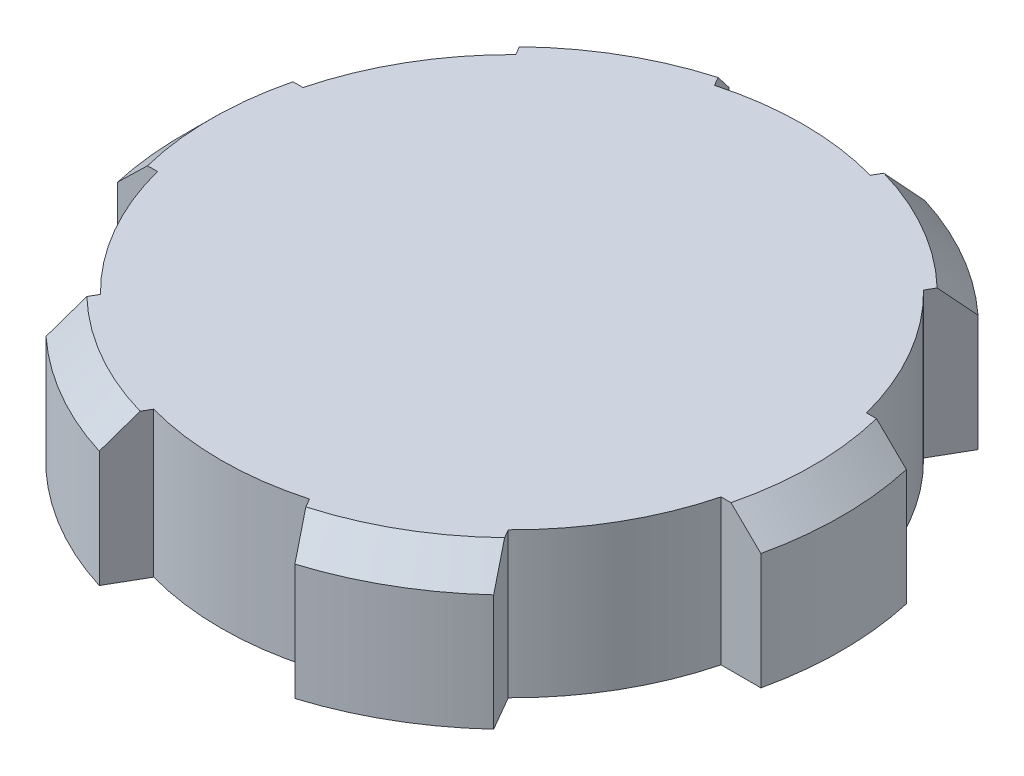
SolidWorks part; units mm, degrees
ref_plane "前视基准面" through (0, 0, 0) normal (0, 0, 1) x (1, 0, 0)
ref_plane "上视基准面" through (0, 0, 0) normal (0, 1, 0) x (1, 0, 0)
ref_plane "右视基准面" through (0, 0, 0) normal (1, 0, 0) x (0, 0, -1)
sketch "草图1" plane through (0, 0, 0) normal (0, 1, 0) x (1, 0, 0)
  circle A0 centre (0, 0) radius 10
  dimension "D1" = 20
extrude "凸台-拉伸1" add sketch "草图1" along normal blind 5
sketch "草图2" plane through (0, 5, 0) normal (0, 1, 0) x (1, 0, 0)
  line L0 (9.6825, 2.5) -> (11.0528, 2.5)
  line L1 (-11.0528, -2.5) -> (-9.6825, -2.5)
  line L3 (-11.0528, 2.5) -> (-9.6825, 2.5)
  line L5 (-11.0528, -2.5) -> (-9.7536, -2.2061) construction
  line L6 (-11.0528, 2.5) -> (-9.7536, 2.2061) construction
  line L7 (9.7536, 2.2061) -> (11.0528, 2.5) construction
  line L8 (9.7536, -2.2061) -> (11.0528, -2.5) construction
  line L9 (9.6825, -2.5) -> (11.0528, -2.5)
  arc A0 (-11.0528, 2.5) -> (-11.0528, -2.5) centre (0, 0) ccw
  arc A1 (11.0528, -2.5) -> (11.0528, 2.5) centre (0, 0) ccw
  arc A2 (-9.6825, 2.5) -> (-9.6825, -2.5) centre (0, 0) ccw
  arc A3 (9.6825, -2.5) -> (9.6825, 2.5) centre (0, 0) ccw
  point P0 (0, 0)
  dimension "D1" = 5
extrude "凸台-拉伸2" add sketch "草图2" against normal up to surface (5 mm away) up to face at (0, 0, 10)
pattern_circular "阵列(圆周)1" count 3 every 60 about axis through (0, 0, 0) along (0, 1, 0) of "凸台-拉伸2"
chamfer "倒角1" distance 1 angle 45 6 edges at (-11.332, 5, 0) (5.666, 5, 9.8138) (-5.666, 5, -9.8138) (-5.666, 5, 9.8138) (5.666, 5, -9.8138) (11.332, 5, 0)
